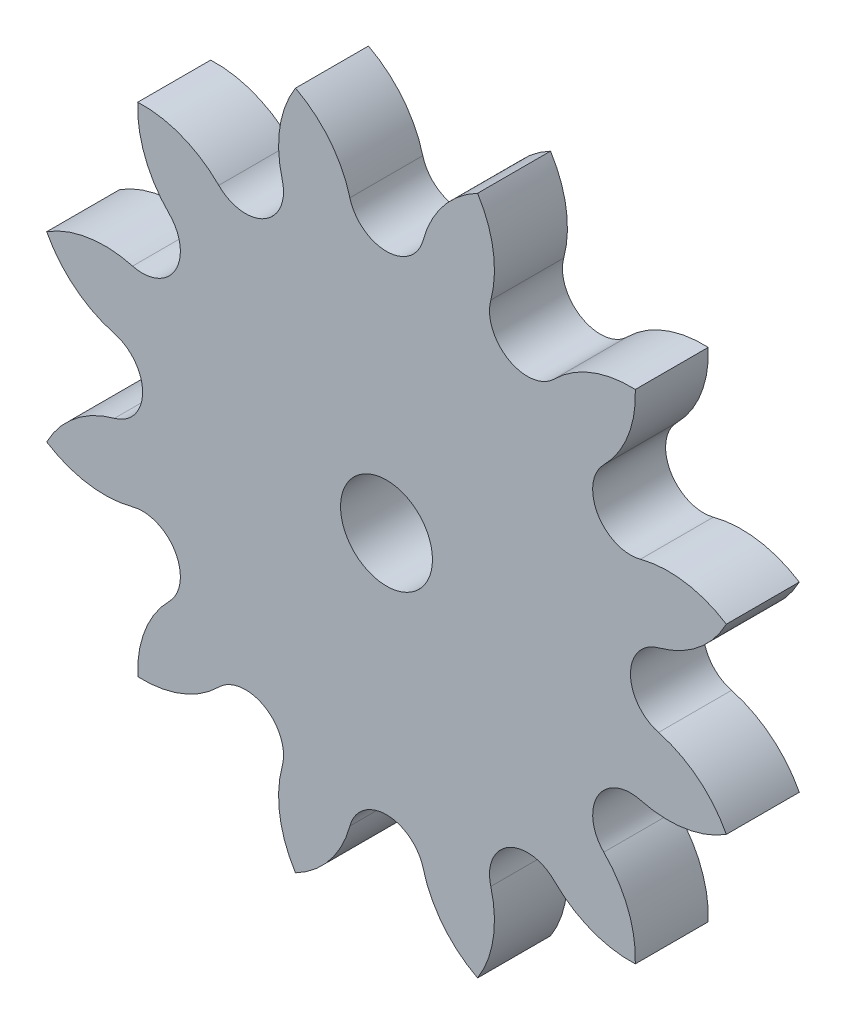
SolidWorks part; units mm, degrees
ref_plane "Front Plane" through (0, 0, 0) normal (0, 0, 1) x (1, 0, 0)
ref_plane "Top Plane" through (0, 0, 0) normal (0, 1, 0) x (1, 0, 0)
ref_plane "Right Plane" through (0, 0, 0) normal (1, 0, 0) x (0, 0, -1)
sketch "Sketch2" plane through (0, 0, 0) normal (0, 0, 1) x (1, 0, 0)
  arc A0 (9.4568, 7.3021) -> (10.8287, 10.828) centre (6.1341, 10.6248) ccw
  arc A1 (10.8287, 10.828) -> (7.3015, 9.4574) centre (10.6231, 6.1336) ccw
  arc A2 (4.5392, 11.0515) -> (7.3015, 9.4574) centre (6.1341, 10.6248) ccw
  arc A3 (4.5392, 11.0515) -> (3.9641, 14.7915) centre (0.0003, 12.2677) ccw
  arc A4 (3.9641, 14.7915) -> (1.5953, 11.8414) centre (6.1337, 10.6234) ccw
  arc A5 (-1.5945, 11.8414) -> (1.5953, 11.8414) centre (0.0004, 12.2681) ccw
  arc A6 (-1.5945, 11.8414) -> (-3.9614, 14.7915) centre (-6.1332, 10.6244) ccw
  arc A7 (-3.9614, 14.7915) -> (-4.5384, 11.0515) centre (0.0011, 12.2657) ccw
  arc A8 (-7.3007, 9.4574) -> (-4.5384, 11.0515) centre (-6.1333, 10.6248) ccw
  arc A9 (-7.3007, 9.4574) -> (-10.8272, 10.8287) centre (-10.6229, 6.1341) ccw
  arc A10 (-10.8272, 10.8287) -> (-9.456, 7.3021) centre (-6.1327, 10.6242) ccw
  arc A11 (-11.0501, 4.5398) -> (-9.456, 7.3021) centre (-10.6234, 6.1347) ccw
  arc A12 (-11.0501, 4.5398) -> (-14.7901, 3.9646) centre (-12.2663, 0.0009) ccw
  arc A13 (-14.7901, 3.9646) -> (-11.84, 1.5959) centre (-10.6219, 6.1343) ccw
  arc A14 (-11.84, -1.5939) -> (-11.84, 1.5959) centre (-12.2667, 0.001) ccw
  arc A15 (-11.84, -1.5939) -> (-14.79, -3.9608) centre (-10.623, -6.1326) ccw
  arc A16 (-14.79, -3.9608) -> (-11.0501, -4.5378) centre (-12.2643, 0.0016) ccw
  arc A17 (-9.456, -7.3001) -> (-11.0501, -4.5378) centre (-10.6234, -6.1327) ccw
  arc A18 (-9.456, -7.3001) -> (-10.8273, -10.8266) centre (-6.1327, -10.6223) ccw
  arc A19 (-10.8273, -10.8266) -> (-7.3007, -9.4554) centre (-10.6228, -6.1321) ccw
  arc A20 (-4.5384, -11.0495) -> (-7.3007, -9.4554) centre (-6.1333, -10.6228) ccw
  arc A21 (-4.5384, -11.0495) -> (-3.9632, -14.7895) centre (0.0005, -12.2657) ccw
  arc A22 (-3.9632, -14.7895) -> (-1.5945, -11.8394) centre (-6.1329, -10.6214) ccw
  arc A23 (1.5953, -11.8394) -> (-1.5945, -11.8394) centre (0.0004, -12.2661) ccw
  arc A24 (1.5953, -11.8394) -> (3.9622, -14.7894) centre (6.134, -10.6224) ccw
  arc A25 (3.9622, -14.7894) -> (4.5392, -11.0495) centre (-0.0002, -12.2637) ccw
  arc A26 (7.3015, -9.4554) -> (4.5392, -11.0495) centre (6.1341, -10.6228) ccw
  arc A27 (7.3015, -9.4554) -> (10.828, -10.8267) centre (10.6237, -6.1321) ccw
  arc A28 (10.828, -10.8267) -> (9.4568, -7.3001) centre (6.1335, -10.6222) ccw
  arc A29 (11.0509, -4.5378) -> (9.4568, -7.3001) centre (10.6242, -6.1327) ccw
  arc A30 (11.0509, -4.5378) -> (14.7909, -3.9626) centre (12.2671, 0.0011) ccw
  arc A31 (14.7909, -3.9626) -> (11.8408, -1.5939) centre (10.6228, -6.1323) ccw
  arc A32 (11.8414, 1.5953) -> (11.8408, -1.5939) centre (12.2689, 0.0006) ccw
  arc A33 (11.8414, 1.5953) -> (14.7915, 3.9622) centre (10.6244, 6.134) ccw
  arc A34 (14.7915, 3.9622) -> (11.0515, 4.5392) centre (12.2657, -0.0002) ccw
  arc A35 (9.4568, 7.3021) -> (11.0515, 4.5392) centre (10.6232, 6.1337) ccw
  circle A36 centre (0, 0) radius 2
  dimension "D1" = 4
extrude "Boss-Extrude2" add sketch "Sketch2" along normal blind 3.175
